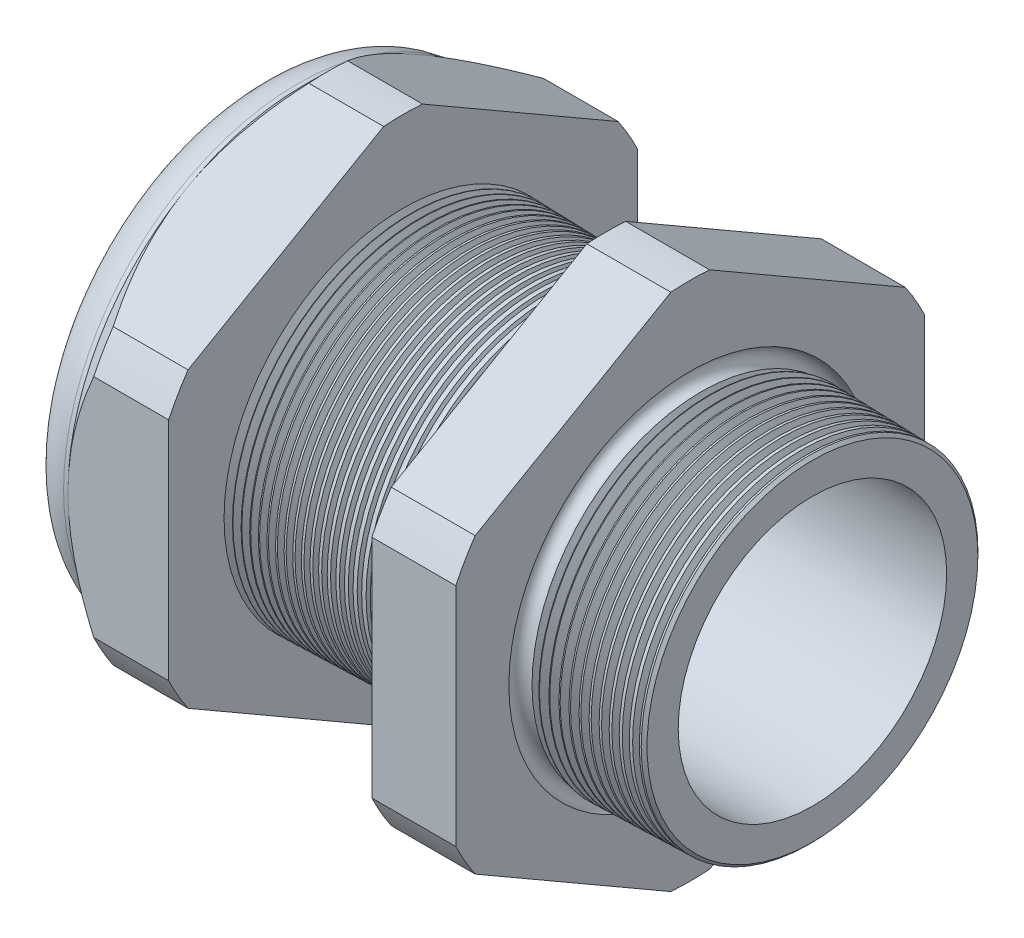
SolidWorks part; units mm, degrees
ref_plane "Front Plane" through (0, 0, 0) normal (0, 0, 1) x (1, 0, 0)
ref_plane "Top Plane" through (0, 0, 0) normal (0, 1, 0) x (1, 0, 0)
ref_plane "Right Plane" through (0, 0, 0) normal (1, 0, 0) x (0, 0, -1)
sketch "Sketch10" plane through (0, 0, 0) normal (0, 0, 1) x (1, 0, 0)
  line L0 (0, 0) -> (-115.3565, 0) construction
  line L1 (-46.736, 12.446) -> (-33.536, 12.446)
  line L2 (3.048, 11.996) -> (3.048, 15.044)
  line L3 (-7.874, 15.33) -> (3.048, 15.044)
  line L4 (-7.874, 41.91) -> (-7.874, 15.33)
  line L5 (-7.874, 41.91) -> (-15.374, 41.91)
  line L6 (-15.374, 41.91) -> (-15.374, 15.5264)
  line L7 (-33.536, 16.002) -> (-15.374, 15.5264)
  line L8 (-33.536, 16.002) -> (-33.536, 41.91)
  line L9 (-33.536, 41.91) -> (-42.536, 41.91)
  line L10 (-42.536, 41.91) -> (-42.536, 20.955)
  line L11 (-42.536, 20.955) -> (-46.736, 20.955)
  line L12 (-46.736, 20.955) -> (-46.736, 12.446)
  line L13 (-33.536, 12.446) -> (3.048, 11.996)
  dimension "D1" = 49.784
  dimension "D2" = 24.892
  dimension "D3" = 1.5
  dimension "D4" = 3.048
  dimension "A" = 32.004
  dimension "D6" = 41.91
  dimension "D8" = 83.82
  dimension "D9" = 4.2
  dimension "D10" = 9
  dimension "D11" = 7.5
  dimension "D" = 10.922
revolve "Revolve2" add sketch "Sketch10" angle 360 about L0
sketch "Sketch12" plane through (-42.536, 0, 0) normal (-1, 0, 0) x (0, 0, 1)
  line L1 (-1.7346, 23.1953) -> (-19.2204, 13.0998)
  line L2 (-20.955, 10.0954) -> (-20.955, -10.0954)
  line L3 (-19.2204, -13.0998) -> (-1.7346, -23.1953)
  line L4 (1.7346, -23.1953) -> (19.2204, -13.0998)
  line L5 (20.955, -10.0954) -> (20.955, 10.0954)
  line L6 (19.2204, 13.0998) -> (1.7346, 23.1953)
  circle A0 centre (0, 0) radius 20.955 construction
  arc A1 (1.7346, 23.1953) -> (-1.7346, 23.1953) centre (0, 0) ccw
  arc A2 (-19.2204, 13.0998) -> (-20.955, 10.0954) centre (0, 0) ccw
  arc A3 (-20.955, -10.0954) -> (-19.2204, -13.0998) centre (0, 0) ccw
  arc A4 (-1.7346, -23.1953) -> (1.7346, -23.1953) centre (0, 0) ccw
  arc A5 (19.2204, -13.0998) -> (20.955, -10.0954) centre (0, 0) ccw
  arc A6 (20.955, 10.0954) -> (19.2204, 13.0998) centre (0, 0) ccw
  dimension "D2" = 46.5201
  dimension "D1" = 41.91
extrude "Cut-Extrude2" cut sketch "Sketch12" against normal through all flip side to cut
fillet "Fillet4" radius 3.81 1 edges at (-46.736, 0, -20.955)
sketch "Sketch19" plane through (-42.536, 0, 0) normal (-1, 0, 0) x (0, 0, 1)
  line L0 (20.955, 0) -> (20.955, 10.0954) construction
  circle A0 centre (0, 0) radius 20.955
extrude "Cut-Extrude3" cut sketch "Sketch19" against normal blind 3.998 draft 45 flip side to cut
chamfer "Chamfer1" distance 0.254 angle 45 1 edges at (3.048, 0, -15.044)
sketch "Sketch21" plane through (-46.736, 0, 0) normal (-1, 0, 0) x (0, 0, 1)
  circle A0 centre (0, 0) radius 12.446
  circle A2 centre (0, 0) radius 12.446 construction
extrude "plug" add sketch "Sketch21" against normal blind 12.7 separate body
sketch "Sketch22" plane through (-46.736, 0, 0) normal (-1, 0, 0) x (0, 0, 1)
  circle A0 centre (0, 0) radius 12.192
  circle A1 centre (0, 0) radius 12.446 construction
  dimension "D1" = 0.254
extrude "Cut-Extrude4" cut sketch "Sketch22" against normal blind 0.508
sketch "Sketch27" plane through (-46.228, 0, 0) normal (-1, 0, 0) x (0, 0, 1)
  line L0 (-4.3624, 0) -> (4.3624, 0) construction
  circle A0 centre (-7.7292, 0) radius 4.445
  circle A1 centre (0, 0) radius 12.192 construction
  dimension "D1" = 0.0178
  dimension "holedia" = 8.89
extrude "plugholes" cut sketch "Sketch27" against normal through all
pattern_circular "CirPattern1" count 4 over 360 about axis through (0, 0, 0) along (1, 0, 0) of "plugholes"
sketch "Sketch28" [suppressed] plane through (-38.354, 0, 0) normal (-1, 0, 0) x (0, 0, 1)
  circle A0 centre (0, 0) radius 1.905
  dimension "midholedia" = 8.89
extrude "midhole" [suppressed] cut sketch "Sketch28" against normal through all
sketch "Sketch29" plane through (0, 0, 0) normal (0, 0, 1) x (1, 0, 0)
  line L0 (-33.536, 16.002) -> (-32.803, 15.9828)
  line L1 (-15.374, 15.5264) -> (-33.536, 16.002) construction
  line L2 (-32.803, 15.9828) -> (-33.1861, 15.3576)
  line L3 (-33.1861, 15.3576) -> (-33.536, 16.002)
  dimension "D1" = 60
  dimension "D2" = 60
  dimension "D3" = 0.635
revolve "Cut-Revolve1" cut sketch "Sketch29" angle 360 about axis through (0, 0, 0) along (-1, 0, 0)
pattern_linear "LPattern1" count 24 spacing 0.762 along (1, 0, 0) of "Cut-Revolve1"
sketch "Sketch30" plane through (0, 0, 0) normal (0, 0, 1) x (1, 0, 0)
  line L0 (-7.874, 15.33) -> (-6.9944, 15.307)
  line L1 (-7.874, 23.1953) -> (-7.874, 13.0998) construction
  line L2 (2.7941, 15.0507) -> (-7.874, 15.33) construction
  line L3 (-6.9944, 15.307) -> (-7.4542, 14.5568)
  line L4 (-7.4542, 14.5568) -> (-7.874, 15.33)
  dimension "D1" = 60
  dimension "D2" = 60
  dimension "D3" = 0.762
revolve "Cut-Revolve2" cut sketch "Sketch30" angle 360 about axis through (0, 0, 0) along (-1, 0, 0)
pattern_linear "LPattern2" count 12 spacing 0.889 along (1, 0, 0) of "Cut-Revolve2"
sketch "Sketch31" [suppressed] plane through (-38.354, 0, 0) normal (-1, 0, 0) x (0, 0, 1)
  line L0 (-1.905, 1.905) -> (1.905, 1.905)
  line L1 (-1.905, -1.905) -> (1.905, -1.905)
  circle A0 centre (0, 0) radius 1.905 construction
  arc A1 (-1.905, 1.905) -> (-1.905, -1.905) centre (-1.905, 0) ccw
  arc A2 (1.905, 1.905) -> (1.905, -1.905) centre (1.905, 0) cw
extrude "Cut-Extrude5" [suppressed] cut sketch "Sketch31" against normal through all
sketch "Sketch32" plane through (0, 0, 0) normal (0, 0, 1) x (1, 0, 0)
  line L0 (-7.874, 23.1953) -> (-7.874, 13.0998) construction
  circle A0 centre (-7.747, 15.33) radius 0.889
  dimension "D2" = 1.778
  dimension "D1" = 0.127
revolve "Cut-Revolve3" cut sketch "Sketch32" angle 360 about axis through (0, 0, 0) along (-1, 0, 0)
